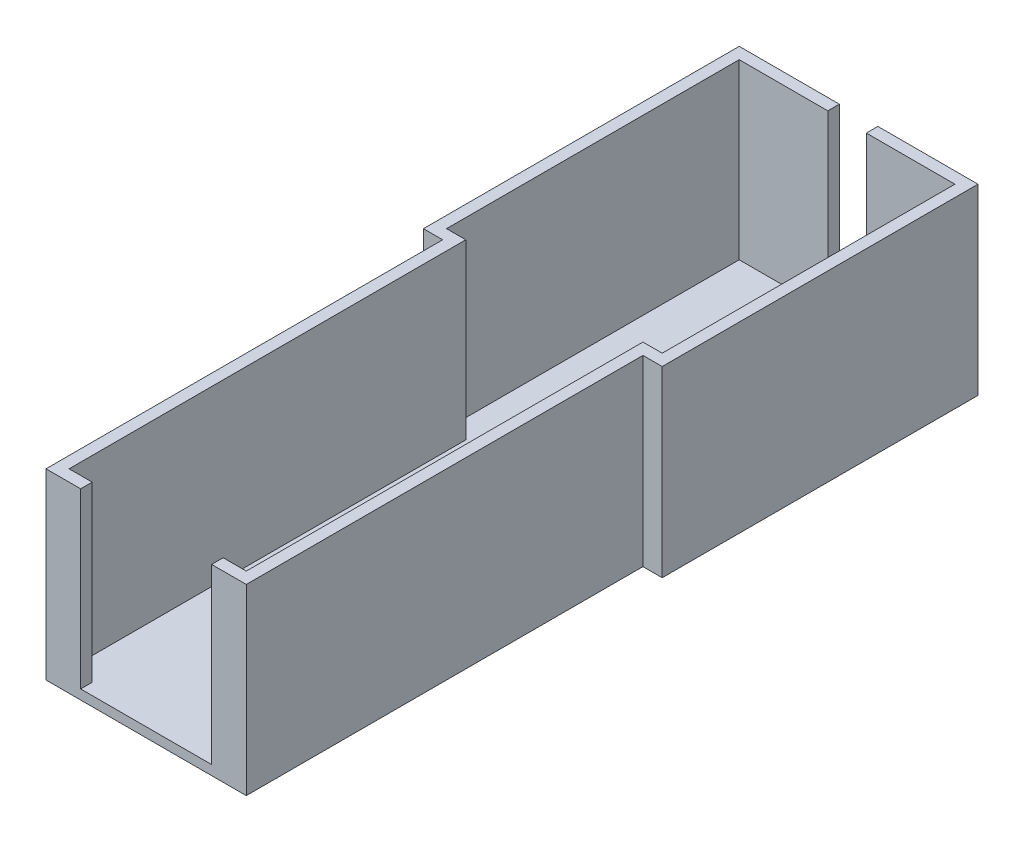
SolidWorks part; units mm, degrees
ref_plane "Front Plane" through (0, 0, 0) normal (0, 0, 1) x (1, 0, 0)
ref_plane "Top Plane" through (0, 0, 0) normal (0, 1, 0) x (1, 0, 0)
ref_plane "Right Plane" through (0, 0, 0) normal (1, 0, 0) x (0, 0, -1)
sketch "Sketch1" plane through (0, 0, 0) normal (0, 1, 0) x (1, 0, 0)
  line L1 (-30.5946, 24.4865) -> (31.4054, 24.4865)
  line L2 (-30.5946, 24.4865) -> (-30.5946, -57.5135)
  line L3 (-30.5946, -57.5135) -> (31.4054, -57.5135)
  line L4 (31.4054, 24.4865) -> (31.4054, -57.5135)
  line L5 (-25.5946, -57.5135) -> (26.4054, -57.5135)
  line L6 (-25.5946, -57.5135) -> (-25.5946, -160.5135)
  line L7 (-25.5946, -160.5135) -> (26.4054, -160.5135)
  line L8 (26.4054, -57.5135) -> (26.4054, -160.5135)
  dimension "D1" = 62
  dimension "D2" = 82
  dimension "D3" = 103
  dimension "D4" = 52
  dimension "D5" = 5
extrude "Boss-Extrude1" add sketch "Sketch1" along normal blind 2.5 contours L8 L3 L6 L7 | L4 L1 L2 L3
sketch "Sketch2" plane through (0, 2.5, 0) normal (0, 1, 0) x (1, 0, 0)
  line L0 (31.4054, 24.4865) -> (31.4054, -57.5135) construction
  line L1 (-30.5946, 24.4865) -> (31.4054, 24.4865)
  line L2 (-30.5946, 24.4865) -> (-30.5946, 21.4865)
  line L3 (-30.5946, 21.4865) -> (31.4054, 21.4865)
  line L4 (31.4054, 24.4865) -> (31.4054, 21.4865)
  line L5 (26.4054, -57.5135) -> (31.4054, -57.5135) construction
  line L6 (31.4054, 24.4865) -> (28.4054, 24.4865)
  line L7 (31.4054, 24.4865) -> (31.4054, -57.5135)
  line L8 (31.4054, -57.5135) -> (28.4054, -57.5135)
  line L9 (28.4054, 24.4865) -> (28.4054, -57.5135)
  line L10 (-30.5946, -57.5135) -> (-25.5946, -57.5135) construction
  line L11 (-30.5946, 24.4865) -> (-27.5946, 24.4865)
  line L12 (-30.5946, 24.4865) -> (-30.5946, -57.5135)
  line L13 (-30.5946, -57.5135) -> (-27.5946, -57.5135)
  line L14 (-27.5946, 24.4865) -> (-27.5946, -57.5135)
  line L15 (26.4054, -57.5135) -> (26.4054, -160.5135) construction
  line L16 (-25.5946, -160.5135) -> (26.4054, -160.5135)
  line L17 (-25.5946, -160.5135) -> (-25.5946, -157.5135)
  line L18 (-25.5946, -157.5135) -> (26.4054, -157.5135)
  line L19 (26.4054, -160.5135) -> (26.4054, -157.5135)
  line L21 (-25.5946, -160.5135) -> (-22.5946, -160.5135)
  line L22 (-25.5946, -160.5135) -> (-25.5946, -54.5135)
  line L23 (-25.5946, -54.5135) -> (-22.5946, -54.5135)
  line L24 (-22.5946, -160.5135) -> (-22.5946, -54.5135)
  line L25 (26.4054, -160.5135) -> (23.4054, -160.5135)
  line L26 (26.4054, -160.5135) -> (26.4054, -54.5135)
  line L27 (26.4054, -54.5135) -> (23.4054, -54.5135)
  line L28 (23.4054, -160.5135) -> (23.4054, -54.5135)
  line L29 (-22.5946, -54.5135) -> (-30.5946, -54.5135)
  line L30 (-22.5946, -54.5135) -> (-22.5946, -57.5135)
  line L31 (-22.5946, -57.5135) -> (-30.5946, -57.5135)
  line L32 (-30.5946, -54.5135) -> (-30.5946, -57.5135)
  line L33 (23.4054, -54.5135) -> (31.4054, -54.5135)
  line L34 (23.4054, -54.5135) -> (23.4054, -57.5135)
  line L35 (23.4054, -57.5135) -> (31.4054, -57.5135)
  line L36 (31.4054, -54.5135) -> (31.4054, -57.5135)
  line M13 (26.4054, -160.5135) -> (26.4054, -57.5135)
  line M14 (26.4054, -57.5135) -> (31.4054, -57.5135)
  line M15 (31.4054, -57.5135) -> (31.4054, 24.4865)
  line M16 (31.4054, 24.4865) -> (-30.5946, 24.4865)
  line M17 (-30.5946, 24.4865) -> (-30.5946, -57.5135)
  line M18 (-30.5946, -57.5135) -> (-25.5946, -57.5135)
  line M19 (-25.5946, -57.5135) -> (-25.5946, -160.5135)
  line M20 (-25.5946, -160.5135) -> (26.4054, -160.5135)
  dimension "D1" = 3
  dimension "D2" = 3
  dimension "D3" = 3
  dimension "D4" = 3
  dimension "D5" = 3
  dimension "D6" = 3
  dimension "D7" = 3
  dimension "D8" = 3
extrude "Boss-Extrude2" add sketch "Sketch2" along normal blind 45 contours L24 L31 L18 M19 | L35 L28 L18 M13 | L9 L33 L7 L3 | L29 L14 L3 M17 | L22 L29 L14 M18 | L31 L24 L23 L22 | L14 L29 L12 M18 | L33 L9 M14 M15 | L33 L26 L9 M14 | L28 L35 L26 L27 | L14 L3 M16 M17 | L9 L3 M16 M15 | L1 L14 L3 L9 | L24 L18 M20 M19 | L16 L28 L18 L24 | L28 L18 M20 M13
sketch "Sketch4" plane through (0, 47.5, 0) normal (0, 1, 0) x (1, 0, 0)
  line L0 (-27.5946, 21.4865) -> (28.4054, 21.4865) construction
  line L1 (-4.5946, 21.4865) -> (5.4054, 21.4865)
  line L2 (-4.5946, 21.4865) -> (-4.5946, 24.4865)
  line L3 (-4.5946, 24.4865) -> (5.4054, 24.4865)
  line L4 (5.4054, 21.4865) -> (5.4054, 24.4865)
  line L5 (31.4054, 24.4865) -> (-30.5946, 24.4865) construction
  line L6 (-30.5946, 24.4865) -> (-30.5946, -57.5135) construction
  line L7 (-25.5946, -160.5135) -> (26.4054, -160.5135) construction
  line L8 (17.4054, -160.5135) -> (-16.5946, -160.5135)
  line L9 (17.4054, -160.5135) -> (17.4054, -157.5135)
  line L10 (17.4054, -157.5135) -> (-16.5946, -157.5135)
  line L11 (-16.5946, -160.5135) -> (-16.5946, -157.5135)
  line L12 (-22.5946, -157.5135) -> (23.4054, -157.5135) construction
  line L13 (-25.5946, -57.5135) -> (-25.5946, -160.5135) construction
  dimension "D1" = 10
  dimension "D2" = 26
  dimension "D3" = 34
  dimension "D4" = 9
extrude "Cut-Extrude1" cut sketch "Sketch4" against normal blind 45
